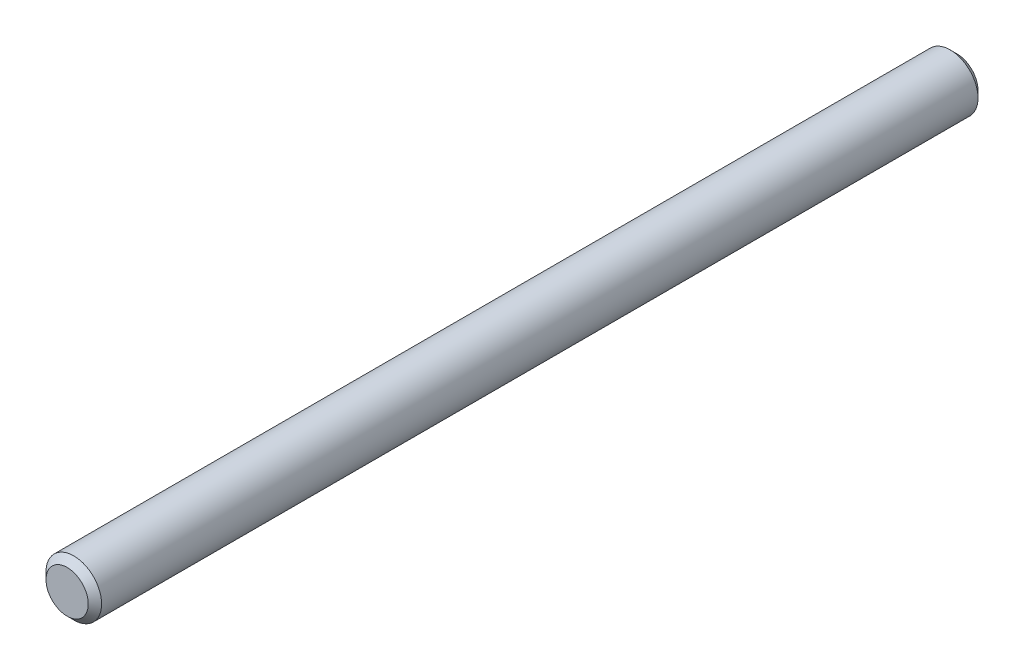
SolidWorks part; units mm, degrees
material "AISI Type 316L stainless steel"
ref_plane "Front Plane" through (0, 0, 0) normal (0, 0, 1) x (1, 0, 0)
ref_plane "Top Plane" through (0, 0, 0) normal (0, 1, 0) x (1, 0, 0)
ref_plane "Right Plane" through (0, 0, 0) normal (1, 0, 0) x (0, 0, -1)
sketch "Sketch1" plane through (0, 0, 0) normal (0, 0, 1) x (1, 0, 0)
  circle A0 centre (0, 0) radius 3.175
  dimension "D1" = 6.35
extrude "Boss-Extrude1" add sketch "Sketch1" along normal blind 101.6
chamfer "Chamfer1" distance 0.762 angle 45 2 edges at (3.175, 0, 0) (3.175, 0, 101.6)
